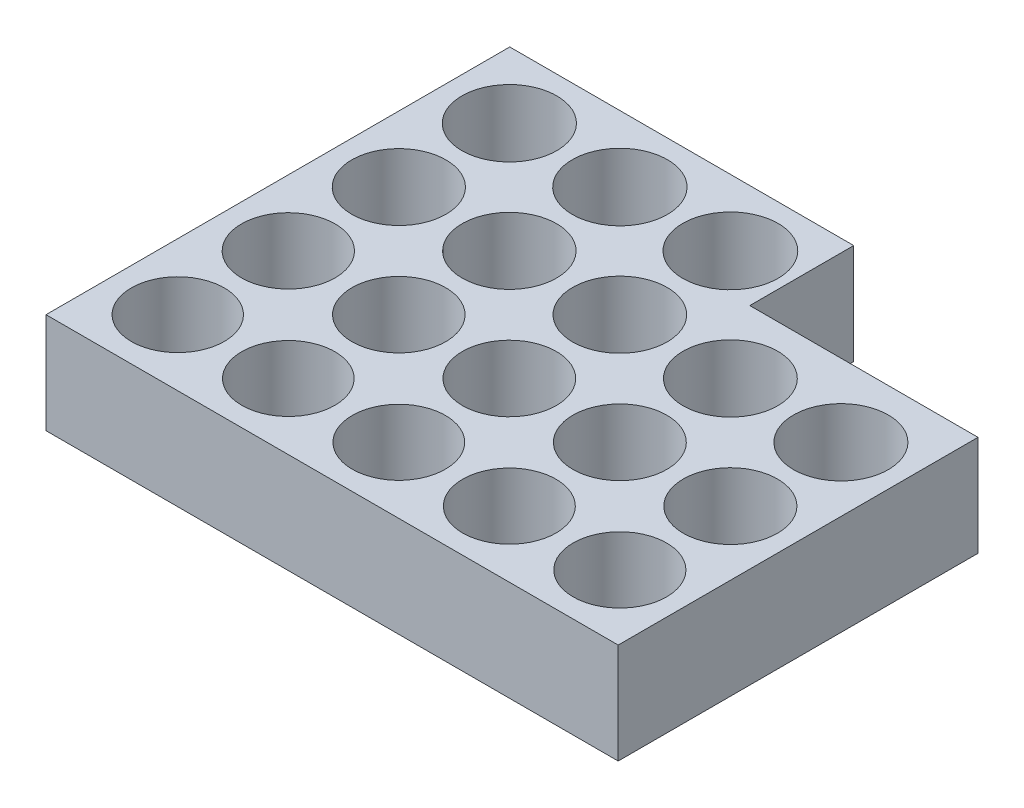
SolidWorks part; units mm, degrees
ref_plane "Front Plane" through (0, 0, 0) normal (0, 0, 1) x (1, 0, 0)
ref_plane "Top Plane" through (0, 0, 0) normal (0, 1, 0) x (1, 0, 0)
ref_plane "Right Plane" through (0, 0, 0) normal (1, 0, 0) x (0, 0, -1)
sketch "Sketch1" plane through (0, 0, 0) normal (0, 1, 0) x (1, 0, 0)
  line L0 (4.9974, 4.9974) -> (0, 4.9974) construction
  line L1 (0, 0) -> (43.3962, 0)
  line L2 (0, 0) -> (0, 35.1714)
  line L3 (0, 35.1714) -> (26.0887, 35.1714)
  line L4 (43.3962, 0) -> (43.3962, 27.2882)
  line L5 (4.9974, 4.9974) -> (4.9974, 0) construction
  line L6 (26.0887, 27.2882) -> (43.3962, 27.2882)
  line L7 (13.3794, 30.1434) -> (13.3794, 21.7614) construction
  line L8 (13.3794, 21.7614) -> (13.3794, 13.3794) construction
  line L9 (13.3794, 13.3794) -> (13.3794, 4.9974) construction
  line L10 (21.7614, 30.1434) -> (21.7614, 21.7614) construction
  line L11 (21.7614, 21.7614) -> (21.7614, 13.3794) construction
  line L12 (21.7614, 13.3794) -> (21.7614, 4.9974) construction
  line L13 (30.1434, 21.7614) -> (30.1434, 13.3794) construction
  line L14 (30.1434, 13.3794) -> (30.1434, 4.9974) construction
  line L15 (38.5254, 21.7614) -> (38.5254, 13.3794) construction
  line L16 (38.5254, 13.3794) -> (38.5254, 4.9974) construction
  line L17 (4.9974, 30.1434) -> (4.9974, 21.7614) construction
  line L18 (4.9974, 21.7614) -> (4.9974, 13.3794) construction
  line L19 (4.9974, 13.3794) -> (4.9974, 4.9974) construction
  line L20 (4.9974, 4.9974) -> (13.3794, 4.9974) construction
  line L21 (13.3794, 4.9974) -> (21.7614, 4.9974) construction
  line L22 (21.7614, 4.9974) -> (30.1434, 4.9974) construction
  line L23 (30.1434, 4.9974) -> (38.5254, 4.9974) construction
  line L24 (26.0887, 35.1714) -> (26.0887, 27.2882)
  circle A2 centre (4.9974, 4.9974) radius 3.525
  circle A3 centre (13.3794, 4.9974) radius 3.53
  circle A4 centre (21.7614, 4.9974) radius 3.535
  circle A5 centre (30.1434, 4.9974) radius 3.54
  circle A6 centre (38.5254, 4.9974) radius 3.545
  circle A7 centre (13.3794, 13.3794) radius 3.555
  circle A8 centre (21.7614, 13.3794) radius 3.56
  circle A9 centre (30.1434, 13.3794) radius 3.565
  circle A10 centre (38.5254, 13.3794) radius 3.57
  circle A11 centre (13.3794, 21.7614) radius 3.58
  circle A12 centre (21.7614, 21.7614) radius 3.585
  circle A13 centre (30.1434, 21.7614) radius 3.59
  circle A14 centre (38.5254, 21.7614) radius 3.595
  circle A15 centre (13.3794, 30.1434) radius 3.605
  circle A16 centre (21.7614, 30.1434) radius 3.615
  circle A19 centre (4.9974, 13.3794) radius 3.55
  circle A20 centre (4.9974, 21.7614) radius 3.575
  circle A21 centre (4.9974, 30.1434) radius 3.6
  point P2 (41.2741, 27.2882)
  dimension "D1" = 7.05
  dimension "D2" = 7.06
  dimension "D3" = 7.07
  dimension "D4" = 7.08
  dimension "D5" = 7.09
  dimension "D6" = 7.1
  dimension "D7" = 7.11
  dimension "D8" = 7.12
  dimension "D9" = 7.13
  dimension "D10" = 7.14
  dimension "D11" = 7.15
  dimension "D12" = 7.16
  dimension "D13" = 7.17
  dimension "D14" = 7.18
  dimension "D15" = 7.19
  dimension "D16" = 7.2
  dimension "D17" = 7.21
  dimension "D18" = 7.23
  dimension "D19" = 8.382
  dimension "D20" = 8.382
extrude "Boss-Extrude1" add sketch "Sketch1" along normal blind 7.62
